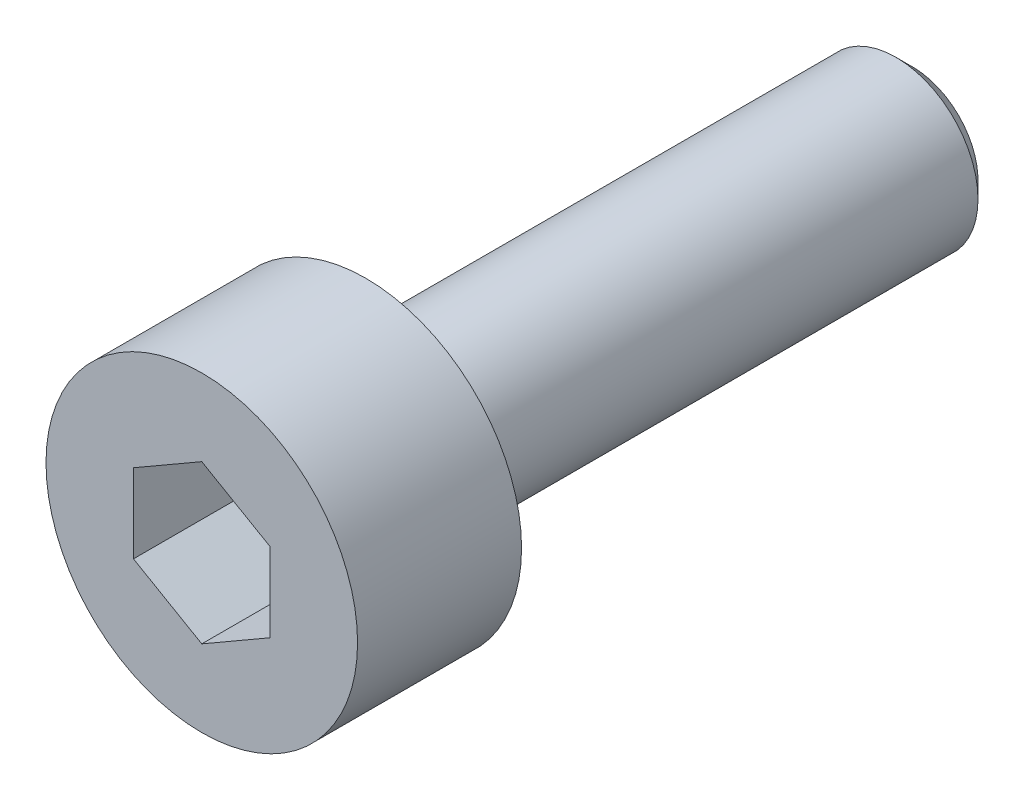
SolidWorks part; units mm, degrees
ref_plane "Front Plane" through (0, 0, 0) normal (0, 0, 1) x (1, 0, 0)
ref_plane "Top Plane" through (0, 0, 0) normal (0, 1, 0) x (1, 0, 0)
ref_plane "Right Plane" through (0, 0, 0) normal (1, 0, 0) x (0, 0, -1)
sketch "Sketch1" plane through (0, 0, 0) normal (0, 0, 1) x (1, 0, 0)
  circle A0 centre (0, 0) radius 2.85
  dimension "D1" = 5.7
extrude "Boss-Extrude1" add sketch "Sketch1" along normal blind 3
sketch "Sketch2" plane through (0, 0, 0) normal (0, 0, -1) x (-1, 0, 0)
  circle A0 centre (0, 0) radius 1.5
  dimension "D1" = 3
extrude "Boss-Extrude2" add sketch "Sketch2" along normal blind 10
chamfer "Chamfer1" distance 0.3 angle 45 1 edges at (-1.5, 0, -10)
sketch "Sketch3" plane through (0, 0, 3) normal (0, 0, 1) x (1, 0, 0)
  line L1 (0, 1.4434) -> (-1.25, 0.7217)
  line L2 (-1.25, 0.7217) -> (-1.25, -0.7217)
  line L3 (-1.25, -0.7217) -> (0, -1.4434)
  line L4 (0, -1.4434) -> (1.25, -0.7217)
  line L5 (1.25, -0.7217) -> (1.25, 0.7217)
  line L6 (1.25, 0.7217) -> (0, 1.4434)
  circle A0 centre (0, 0) radius 1.25 construction
  dimension "D1" = 2.5
extrude "Cut-Extrude1" cut sketch "Sketch3" against normal blind 2
